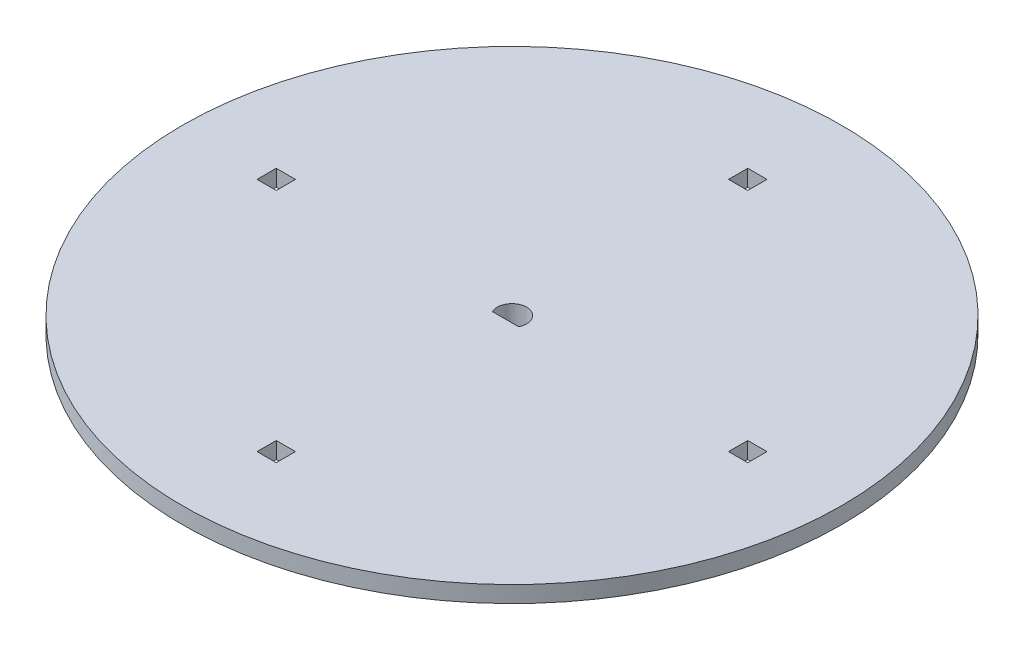
SolidWorks part; units mm, degrees
ref_plane "Front Plane" through (0, 0, 0) normal (0, 0, 1) x (1, 0, 0)
ref_plane "Top Plane" through (0, 0, 0) normal (0, 1, 0) x (1, 0, 0)
ref_plane "Right Plane" through (0, 0, 0) normal (1, 0, 0) x (0, 0, -1)
sketch "Sketch1" plane through (0, 0, 0) normal (0, 0, 1) x (1, 0, 0)
  line L1 (0, 0) -> (1.9579, 0)
  line L2 (0, 0) -> (0, -7.1086)
  line L3 (0, -7.1086) -> (3.0734, -7.1086)
  line L4 (3.0734, -3) -> (3.0734, -7.1086)
  line L5 (0, 0) -> (60, 0)
  line L6 (0, 0) -> (0, -2.015)
  line L7 (3.0734, -3) -> (60, -3)
  line L8 (60, 0) -> (60, -3)
  dimension "D1" = 60
  dimension "D2" = 7.1086
  dimension "D3" = 3
  dimension "D4" = 3.0734
revolve "Revolve1" add sketch "Sketch1" angle 360 about L2
sketch "Sketch2" plane through (0, 0, 0) normal (0, 1, 0) x (1, 0, 0)
  line L0 (2.3777, -1.17) -> (-2.3777, -1.17)
  line L1 (-41.17, -1.75) -> (-44.67, -1.75)
  line L6 (1.75, -41.17) -> (-1.75, -41.17)
  line L7 (1.75, -41.17) -> (1.75, -44.67)
  line L8 (1.75, -44.67) -> (-1.75, -44.67)
  line L9 (-1.75, -41.17) -> (-1.75, -44.67)
  line L10 (1.75, -41.17) -> (-1.75, -44.67) construction
  line L11 (1.75, -44.67) -> (-1.75, -41.17) construction
  line L12 (-41.17, -1.75) -> (-41.17, 1.75)
  line L13 (-41.17, 1.75) -> (-44.67, 1.75)
  line L14 (-44.67, -1.75) -> (-44.67, 1.75)
  line L15 (-1.75, 41.17) -> (-1.75, 44.67)
  line L16 (-1.75, 41.17) -> (1.75, 41.17)
  line L17 (1.75, 41.17) -> (1.75, 44.67)
  line L18 (-1.75, 44.67) -> (1.75, 44.67)
  line L19 (41.17, 1.75) -> (44.67, 1.75)
  line L20 (41.17, 1.75) -> (41.17, -1.75)
  line L21 (41.17, -1.75) -> (44.67, -1.75)
  line L22 (44.67, 1.75) -> (44.67, -1.75)
  arc A0 (2.3777, -1.17) -> (-2.3777, -1.17) centre (0, 0) ccw
  point P1 (0, -42.92)
  point P5 (0, 2.65)
  point P25 (0, 0)
  dimension "D1" = 5.3
  dimension "D2" = 3.82
  dimension "D3" = 40
  dimension "D4" = 3.5
  dimension "D5" = 4
extrude "Cut-Extrude1" cut sketch "Sketch2" against normal through all
